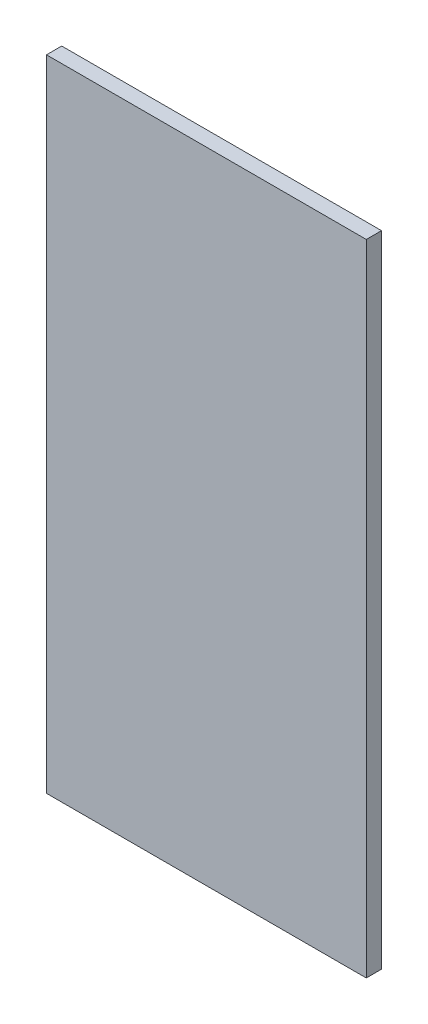
SolidWorks part; units mm, degrees
ref_plane "Front Plane" through (0, 0, 0) normal (0, 0, 1) x (1, 0, 0)
ref_plane "Top Plane" through (0, 0, 0) normal (0, 1, 0) x (1, 0, 0)
ref_plane "Right Plane" through (0, 0, 0) normal (1, 0, 0) x (0, 0, -1)
sketch "Sketch1" plane through (0, 0, 0) normal (0, 0, 1) x (1, 0, 0)
  line L1 (26.67, 53.34) -> (-26.67, 53.34)
  line L2 (26.67, 53.34) -> (26.67, -53.34)
  line L3 (26.67, -53.34) -> (-26.67, -53.34)
  line L4 (-26.67, 53.34) -> (-26.67, -53.34)
  line L5 (26.67, 53.34) -> (-26.67, -53.34) construction
  line L6 (26.67, -53.34) -> (-26.67, 53.34) construction
  point P0 (0, 0)
  dimension "D1" = 53.34
  dimension "D2" = 106.68
extrude "Boss-Extrude2" add sketch "Sketch1" along normal mid plane 2.54
